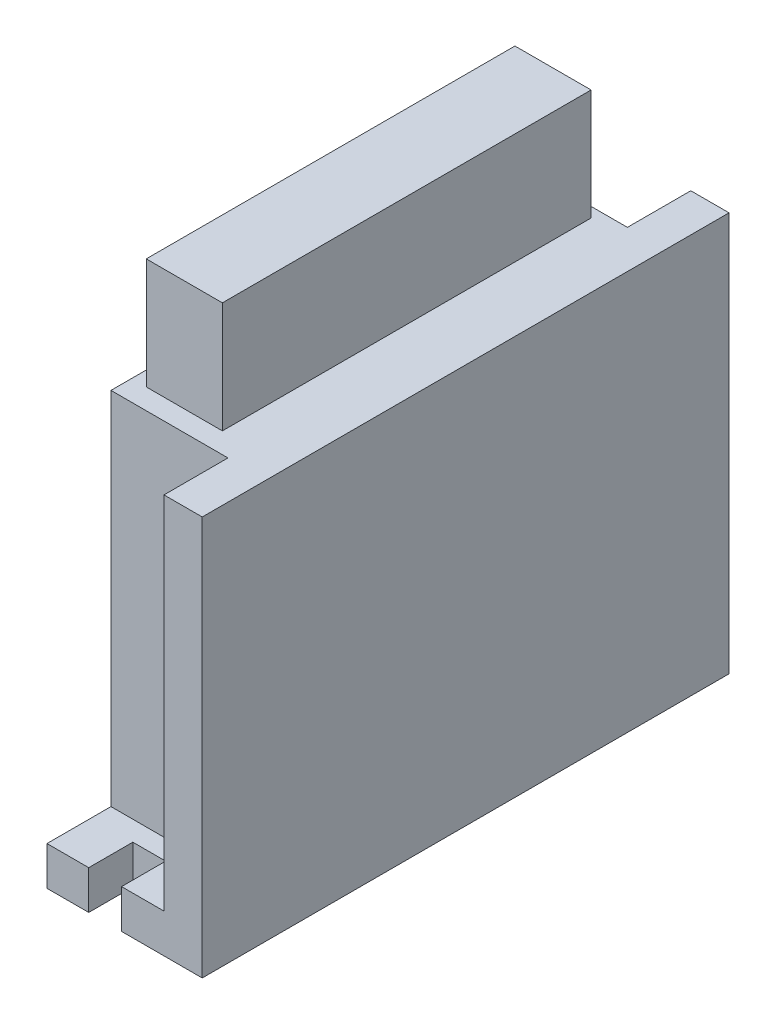
SolidWorks part; units mm, degrees
ref_plane "Front Plane" through (0, 0, 0) normal (0, 0, 1) x (1, 0, 0)
ref_plane "Top Plane" through (0, 0, 0) normal (0, 1, 0) x (1, 0, 0)
ref_plane "Right Plane" through (0, 0, 0) normal (1, 0, 0) x (0, 0, -1)
sketch "Sketch1" plane through (0, 0, 0) normal (0, 1, 0) x (1, 0, 0)
  line L1 (-8.8541, 43.6708) -> (19.1459, 43.6708)
  line L2 (-8.8541, 43.6708) -> (-8.8541, -51.3292)
  line L3 (-8.8541, -51.3292) -> (19.1459, -51.3292)
  line L4 (19.1459, 43.6708) -> (19.1459, -51.3292)
  dimension "D1" = 95
  dimension "D2" = 28
extrude "Boss-Extrude1" add sketch "Sketch1" along normal blind 72
sketch "Sketch2" plane through (0, 72, 0) normal (0, 1, 0) x (1, 0, 0)
  line L1 (-6.2102, 30.4185) -> (7.5204, 30.4185)
  line L2 (-6.2102, 30.4185) -> (-6.2102, -36.0676)
  line L3 (-6.2102, -36.0676) -> (7.5204, -36.0676)
  line L4 (7.5204, 30.4185) -> (7.5204, -36.0676)
extrude "Boss-Extrude2" add sketch "Sketch2" along normal blind 20 contours L2 L1 L4 L3
sketch "Sketch3" plane through (0, 72, 0) normal (0, 1, 0) x (1, 0, 0)
  line L1 (-8.8541, -51.3292) -> (12.2491, -51.3292)
  line L2 (-8.8541, -51.3292) -> (-8.8541, -39.7892)
  line L3 (-8.8541, -39.7892) -> (12.2491, -39.7892)
  line L4 (12.2491, -51.3292) -> (12.2491, -39.7892)
  line L5 (-8.8541, 43.6708) -> (12.2491, 43.6708)
  line L6 (-8.8541, 43.6708) -> (-8.8541, 32.2365)
  line L7 (-8.8541, 32.2365) -> (12.2491, 32.2365)
  line L8 (12.2491, 43.6708) -> (12.2491, 32.2365)
extrude "Cut-Extrude1" cut sketch "Sketch3" against normal blind 65
sketch "Sketch4" plane through (0, 7, 0) normal (0, 1, 0) x (1, 0, 0)
  line L0 (-8.8541, -51.3292) -> (12.2491, -51.3292) construction
  line L1 (-1.3231, -51.3292) -> (4.5979, -51.3292)
  line L2 (-1.3231, -51.3292) -> (-1.3231, -43.3738)
  line L3 (-1.3231, -43.3738) -> (4.5979, -43.3738)
  line L4 (4.5979, -51.3292) -> (4.5979, -43.3738)
  line L5 (19.1459, -3.8292) -> (-24.9921, -3.8292) construction
  line L6 (19.1459, -51.3292) -> (19.1459, 43.6708) construction
  line L7 (-1.3231, 35.7154) -> (4.5979, 35.7154)
  line L8 (4.5979, 43.6708) -> (4.5979, 35.7154)
  line L9 (-1.3231, 43.6708) -> (4.5979, 43.6708)
  line L10 (-1.3231, 43.6708) -> (-1.3231, 35.7154)
extrude "Cut-Extrude2" cut sketch "Sketch4" against normal blind 65
